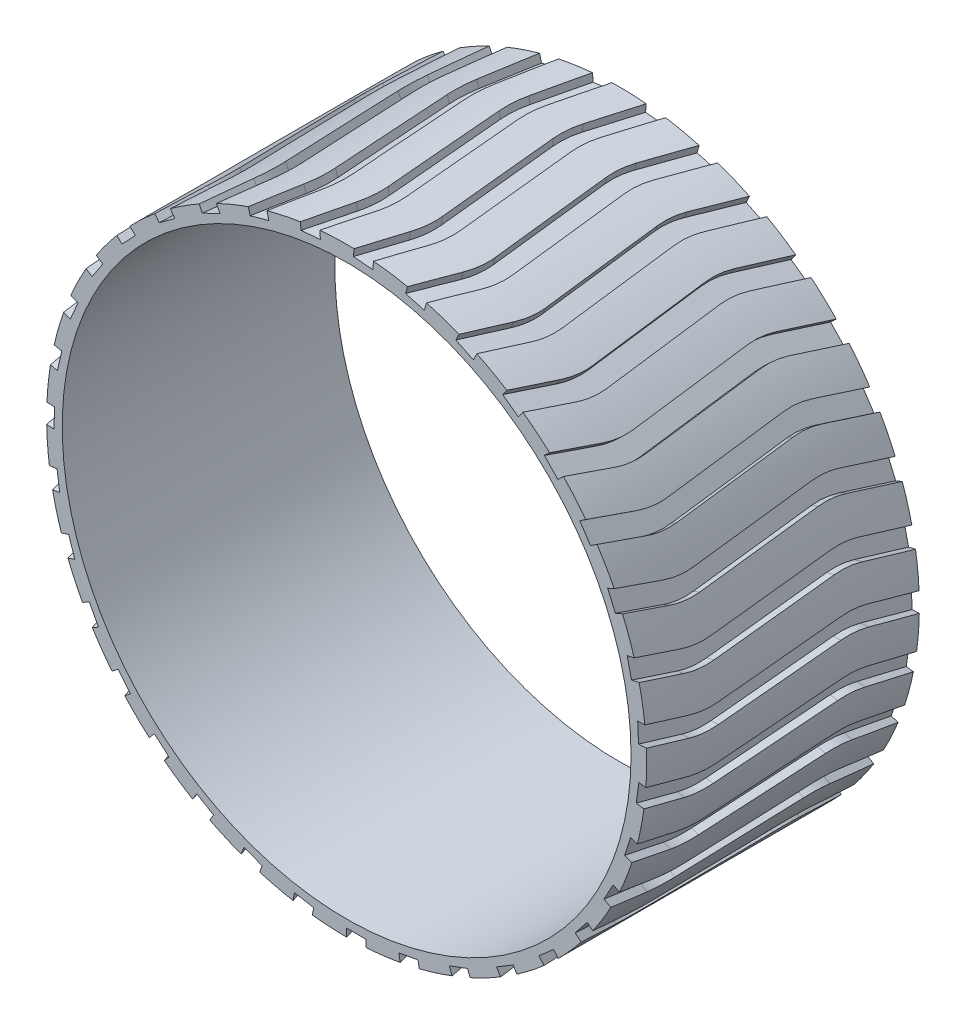
SolidWorks part; units mm, degrees
material "BUTYL"
ref_plane "Front Plane" through (0, 0, 0) normal (0, 0, 1) x (1, 0, 0)
ref_plane "Top Plane" through (0, 0, 0) normal (0, 1, 0) x (1, 0, 0)
ref_plane "Right Plane" through (0, 0, 0) normal (1, 0, 0) x (0, 0, -1)
sketch "Sketch1" plane through (0, 0, 0) normal (0, 0, 1) x (1, 0, 0)
  circle A0 centre (0, 0) radius 77
  circle A1 centre (0, 0) radius 73
  dimension "D1" = 154
  dimension "D2" = 146
extrude "Boss-Extrude1" add sketch "Sketch1" along normal blind 70
sketch "Sketch3" plane through (0, 0, 0) normal (0, 1, 0) x (1, 0, 0)
  line L0 (0, 0) -> (0, -70) construction
  line L4 (-77, -70) -> (77, -70) construction
  line L6 (0, 0) -> (-5, 0)
  line L7 (77, 0) -> (-77, 0) construction
  line L8 (-5, 0) -> (-1.5163, -13.0658)
  line L9 (-0.9296, -20.0968) -> (-3.9003, -51.5865)
  line L10 (-3.189, -59.0638) -> (0, -70)
  line L11 (0, 0) -> (3.4174, -12.817)
  line L12 (4.0041, -19.848) -> (1.0319, -51.3538)
  line L13 (1.7431, -58.831) -> (5, -70)
  line L14 (5, -70) -> (0, -70)
  arc A0 (3.4174, -12.817) -> (4.0041, -19.848) centre (-15.9075, -17.9695) cw
  arc A1 (-1.5163, -13.0658) -> (-0.9296, -20.0968) centre (-20.8412, -18.2183) cw
  arc A2 (1.0319, -51.3538) -> (1.7431, -58.831) centre (20.9435, -53.2322) ccw
  arc A3 (-3.9003, -51.5865) -> (-3.189, -59.0638) centre (16.0113, -53.4649) ccw
  point P6 (0, -35)
  dimension "D3" = 20
  dimension "D1" = 5
  dimension "D2" = 5
extrude "Cut-Extrude2" cut sketch "Sketch3" against normal blind 5 from offset 75 offset against normal yes
pattern_circular "CirPattern1" count 35 over 360 about axis through (0, 0, 0) along (0, 0, 1) of "Cut-Extrude2"
